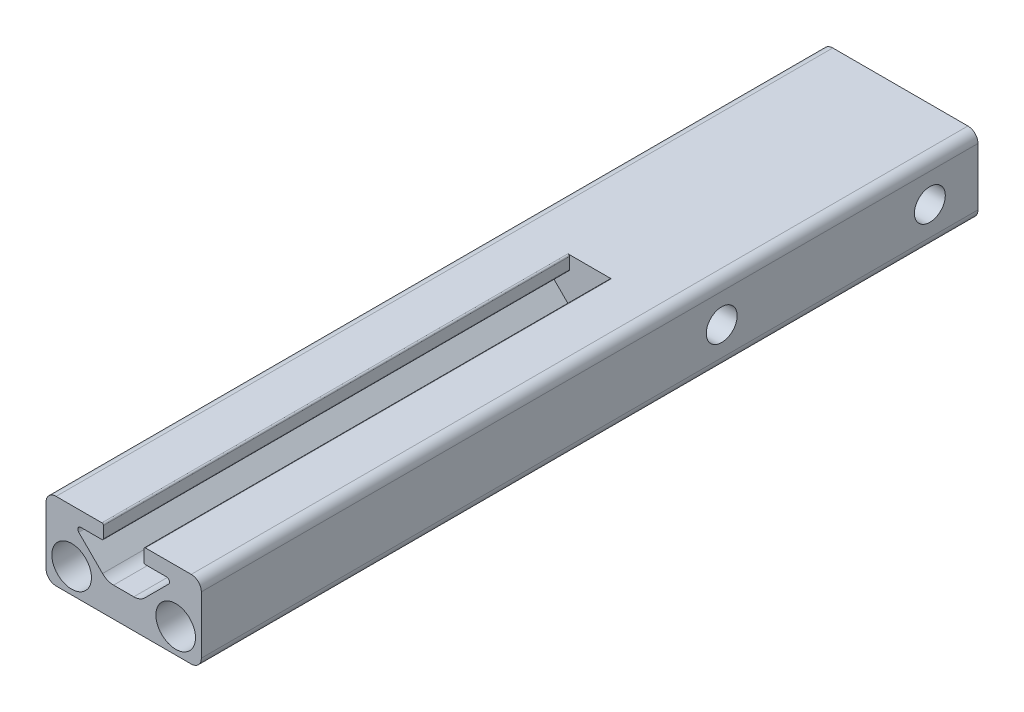
SolidWorks part; units mm, degrees
other "Imported1" parameters "D1"=76.2, "Length"=76.2
ref_plane "Front" through (0, 0, 0) normal (0, 0, 1) x (1, 0, 0)
ref_plane "Top" through (0, 0, 0) normal (0, 1, 0) x (1, 0, 0)
ref_plane "Right" through (0, 0, 0) normal (1, 0, 0) x (0, 0, -1)
sketch "Sketch1" plane through (0, 0, 0) normal (0, 0, 1) x (1, 0, 0)
  line L0 (-3.302, 12.7) -> (3.302, 12.7) construction
  line L1 (-7.493, 9.8209) -> (7.493, 9.8209) construction
  line L2 (-11.049, 12.7) -> (-3.302, 12.7)
  line L3 (3.302, 12.7) -> (11.049, 12.7)
  line L4 (11.049, 0) -> (-11.049, 0)
  line L5 (-8.509, 4.064) -> (8.509, 4.064) construction
  line L6 (-3.302, 12.7) -> (-3.302, 10.3289)
  line L7 (3.302, 12.7) -> (3.302, 10.3289)
  line L28 (-12.7, 11.049) -> (-12.7, 1.651)
  line L32 (12.7, 1.651) -> (12.7, 11.049)
  line L35 (3.302, 10.3289) -> (6.985, 10.3289)
  line L36 (7.3442, 9.4617) -> (3.4525, 5.5699)
  line L37 (1.6565, 4.826) -> (-1.6565, 4.826)
  line L38 (-3.4525, 5.5699) -> (-7.3442, 9.4617)
  line L39 (-6.985, 10.3289) -> (-3.302, 10.3289)
  circle A0 centre (-8.509, 4.064) radius 3.2385
  circle A1 centre (8.509, 4.064) radius 3.2385
  arc A36 (-12.7, 1.651) -> (-11.049, 0) centre (-11.049, 1.651) ccw
  arc A41 (11.049, 0) -> (12.7, 1.651) centre (11.049, 1.651) ccw
  arc A42 (12.7, 11.049) -> (11.049, 12.7) centre (11.049, 11.049) ccw
  arc A46 (7.3442, 9.4617) -> (6.985, 10.3289) centre (6.985, 9.8209) ccw
  arc A47 (1.6565, 4.826) -> (3.4525, 5.5699) centre (1.6565, 7.366) ccw
  arc A48 (-3.4525, 5.5699) -> (-1.6565, 4.826) centre (-1.6565, 7.366) ccw
  arc A49 (-6.985, 10.3289) -> (-7.3442, 9.4617) centre (-6.985, 9.8209) ccw
  arc A53 (-11.049, 12.7) -> (-12.7, 11.049) centre (-11.049, 11.049) ccw
  point P5 (0, 4.064)
  point P8 (0, 0)
  point P10 (0, 4.826)
  point P11 (0, 9.8209)
  point P13 (0, 12.7)
  dimension "D6" = 1.651
  dimension "D7" = 0.508
  dimension "D8" = 8.636
  dimension "D9" = 6.477
  dimension "D12" = 2.54
  dimension "D1" = 6.604
  dimension "D2" = 14.986
  dimension "D3" = 17.018
  dimension "D4" = 25.4
  dimension "D5" = 12.7
  dimension "D10" = 7.874
  dimension "D11" = 2.3711
  dimension "D13" = 45
sketch "Sketch2" plane through (0, 0, 0) normal (1, 0, 0) x (0, 0, -1)
  line L0 (38.1, 0) -> (-38.1, 0) construction
  point P4 (0, 0)
sketch "Sketch3" plane through (0, 0, 0) normal (0, 0, 1) x (1, 0, 0)
  line L0 (-11.049, 12.7) -> (-3.302, 12.7) construction
  line L1 (-3.302, 12.7) -> (-3.302, 10.3289) construction
  line L2 (-6.985, 10.3289) -> (-3.302, 10.3289) construction
  line L3 (-3.4525, 5.5699) -> (-7.3442, 9.4617) construction
  line L4 (1.6565, 4.826) -> (-1.6565, 4.826) construction
  line L5 (7.3442, 9.4617) -> (3.4525, 5.5699) construction
  line L6 (3.302, 10.3289) -> (6.985, 10.3289) construction
  line L7 (3.302, 12.7) -> (3.302, 10.3289) construction
  line L8 (3.302, 12.7) -> (11.049, 12.7) construction
  line L9 (12.7, 1.651) -> (12.7, 11.049) construction
  line L10 (11.049, 0) -> (-11.049, 0) construction
  line L11 (-12.7, 11.049) -> (-12.7, 1.651) construction
  line L12 (-11.049, 12.7) -> (-3.302, 12.7)
  line L13 (-3.302, 12.7) -> (-3.302, 10.3289)
  line L14 (-6.985, 10.3289) -> (-3.302, 10.3289)
  line L15 (-3.4525, 5.5699) -> (-7.3442, 9.4617)
  line L16 (1.6565, 4.826) -> (-1.6565, 4.826)
  line L17 (7.3442, 9.4617) -> (3.4525, 5.5699)
  line L18 (3.302, 10.3289) -> (6.985, 10.3289)
  line L19 (3.302, 12.7) -> (3.302, 10.3289)
  line L20 (3.302, 12.7) -> (11.049, 12.7)
  line L21 (12.7, 1.651) -> (12.7, 11.049)
  line L22 (11.049, 0) -> (-11.049, 0)
  line L23 (-12.7, 11.049) -> (-12.7, 1.651)
  circle A0 centre (8.509, 4.064) radius 3.2385 construction
  circle A1 centre (-8.509, 4.064) radius 3.2385 construction
  arc A2 (-6.985, 10.3289) -> (-7.3442, 9.4617) centre (-6.985, 9.8209) ccw construction
  arc A3 (-3.4525, 5.5699) -> (-1.6565, 4.826) centre (-1.6565, 7.366) ccw construction
  arc A4 (1.6565, 4.826) -> (3.4525, 5.5699) centre (1.6565, 7.366) ccw construction
  arc A5 (7.3442, 9.4617) -> (6.985, 10.3289) centre (6.985, 9.8209) ccw construction
  arc A6 (12.7, 11.049) -> (11.049, 12.7) centre (11.049, 11.049) ccw construction
  arc A7 (11.049, 0) -> (12.7, 1.651) centre (11.049, 1.651) ccw construction
  arc A8 (-12.7, 1.651) -> (-11.049, 0) centre (-11.049, 1.651) ccw construction
  arc A9 (-11.049, 12.7) -> (-12.7, 11.049) centre (-11.049, 11.049) ccw construction
  circle A10 centre (8.509, 4.064) radius 3.2385
  circle A11 centre (-8.509, 4.064) radius 3.2385
  arc A12 (-6.985, 10.3289) -> (-7.3442, 9.4617) centre (-6.985, 9.8209) ccw
  arc A13 (-3.4525, 5.5699) -> (-1.6565, 4.826) centre (-1.6565, 7.366) ccw
  arc A14 (1.6565, 4.826) -> (3.4525, 5.5699) centre (1.6565, 7.366) ccw
  arc A15 (7.3442, 9.4617) -> (6.985, 10.3289) centre (6.985, 9.8209) ccw
  arc A16 (12.7, 11.049) -> (11.049, 12.7) centre (11.049, 11.049) ccw
  arc A17 (11.049, 0) -> (12.7, 1.651) centre (11.049, 1.651) ccw
  arc A18 (-12.7, 1.651) -> (-11.049, 0) centre (-11.049, 1.651) ccw
  arc A19 (-11.049, 12.7) -> (-12.7, 11.049) centre (-11.049, 11.049) ccw
extrude "Boss-Extrude1" add sketch "Sketch3" along normal mid plane 76.2
fillet "Fillet1" radius 0.254 4 edges at (3.302, 10.3289, 0) (3.302, 12.7, 0) (-3.302, 10.3289, 0) (-3.302, 12.7, 0)
sketch "Sketch4" plane through (0, 0, -38.1) normal (0, 0, -1) x (-1, 0, 0)
  line L12 (-6.985, 10.3289) -> (-3.556, 10.3289)
  line L13 (-3.302, 10.5829) -> (-3.302, 12.446)
  line L14 (-3.556, 12.7) -> (-11.049, 12.7)
  line L15 (-12.7, 11.049) -> (-12.7, 1.651)
  line L16 (-11.049, 0) -> (11.049, 0)
  line L17 (12.7, 1.651) -> (12.7, 11.049)
  line L18 (11.049, 12.7) -> (3.556, 12.7)
  line L19 (3.302, 12.446) -> (3.302, 10.5829)
  line L20 (3.556, 10.3289) -> (6.985, 10.3289)
  line L21 (7.3442, 9.4617) -> (3.4525, 5.5699)
  line L22 (1.6565, 4.826) -> (-1.6565, 4.826)
  line L23 (-3.4525, 5.5699) -> (-7.3442, 9.4617)
  line L26 (3.556, 12.7) -> (-11.049, 12.7)
  line L27 (-12.7, 11.049) -> (-12.7, 1.651)
  line L28 (-11.049, 0) -> (11.049, 0)
  line L29 (12.7, 1.651) -> (12.7, 11.049)
  line L30 (11.049, 12.7) -> (3.556, 12.7)
  arc A12 (-3.556, 10.3289) -> (-3.302, 10.5829) centre (-3.556, 10.5829) ccw
  arc A13 (-3.302, 12.446) -> (-3.556, 12.7) centre (-3.556, 12.446) ccw
  arc A14 (-11.049, 12.7) -> (-12.7, 11.049) centre (-11.049, 11.049) ccw
  arc A15 (-12.7, 1.651) -> (-11.049, 0) centre (-11.049, 1.651) ccw
  arc A16 (11.049, 0) -> (12.7, 1.651) centre (11.049, 1.651) ccw
  arc A17 (12.7, 11.049) -> (11.049, 12.7) centre (11.049, 11.049) ccw
  arc A18 (3.556, 12.7) -> (3.302, 12.446) centre (3.556, 12.446) ccw
  arc A19 (3.302, 10.5829) -> (3.556, 10.3289) centre (3.556, 10.5829) ccw
  arc A20 (7.3442, 9.4617) -> (6.985, 10.3289) centre (6.985, 9.8209) ccw
  arc A21 (1.6565, 4.826) -> (3.4525, 5.5699) centre (1.6565, 7.366) ccw
  arc A22 (-3.4525, 5.5699) -> (-1.6565, 4.826) centre (-1.6565, 7.366) ccw
  arc A23 (-6.985, 10.3289) -> (-7.3442, 9.4617) centre (-6.985, 9.8209) ccw
  arc A26 (-11.049, 12.7) -> (-12.7, 11.049) centre (-11.049, 11.049) ccw
  arc A27 (-12.7, 1.651) -> (-11.049, 0) centre (-11.049, 1.651) ccw
  arc A28 (11.049, 0) -> (12.7, 1.651) centre (11.049, 1.651) ccw
  arc A29 (12.7, 11.049) -> (11.049, 12.7) centre (11.049, 11.049) ccw
  dimension "D1" = 0
extrude "Boss-Extrude2" add sketch "Sketch4" along normal blind 50.8
hole_wizard "#8 (0.199) Diameter Hole8" positions "Sketch13" profile "Sketch14" hole size "#8" standard "ANSI Inch" end condition through all
sketch "Sketch13" plane through (12.7, 0, 0) normal (1, 0, 0) x (0, 0, -1)
  line L0 (88.9, 11.049) -> (88.9, 1.651) construction
  line L1 (88.9, 11.049) -> (88.9, 1.651) construction
  point P0 (81.026, 6.35)
  point P6 (88.9, 6.35)
  dimension "D1" = 7.874
sketch "Sketch14" plane through (12.7, 6.35, -81.026) normal (0, 1, 0) x (0, 0, -1)
  line L0 (0, 0) -> (0, 25.4)
  line L1 (0, 25.4) -> (2.5273, 25.4)
  line L2 (2.5273, 25.4) -> (2.5273, 0)
  line L5 (2.5273, 0) -> (0, 0)
  line L11 (0, -6.35) -> (0, 107.95) construction
  dimension "Thru Hole Dia." = 5.0546
  dimension "Thru Hole Depth" = 25.4
pattern_linear "LPattern1" count 2 spacing 34.036 along (0, 0, 1) of "#8 (0.199) Diameter Hole8"
equation "\"D1@Boss-Extrude1\"=\"Length@Sketch2\""
